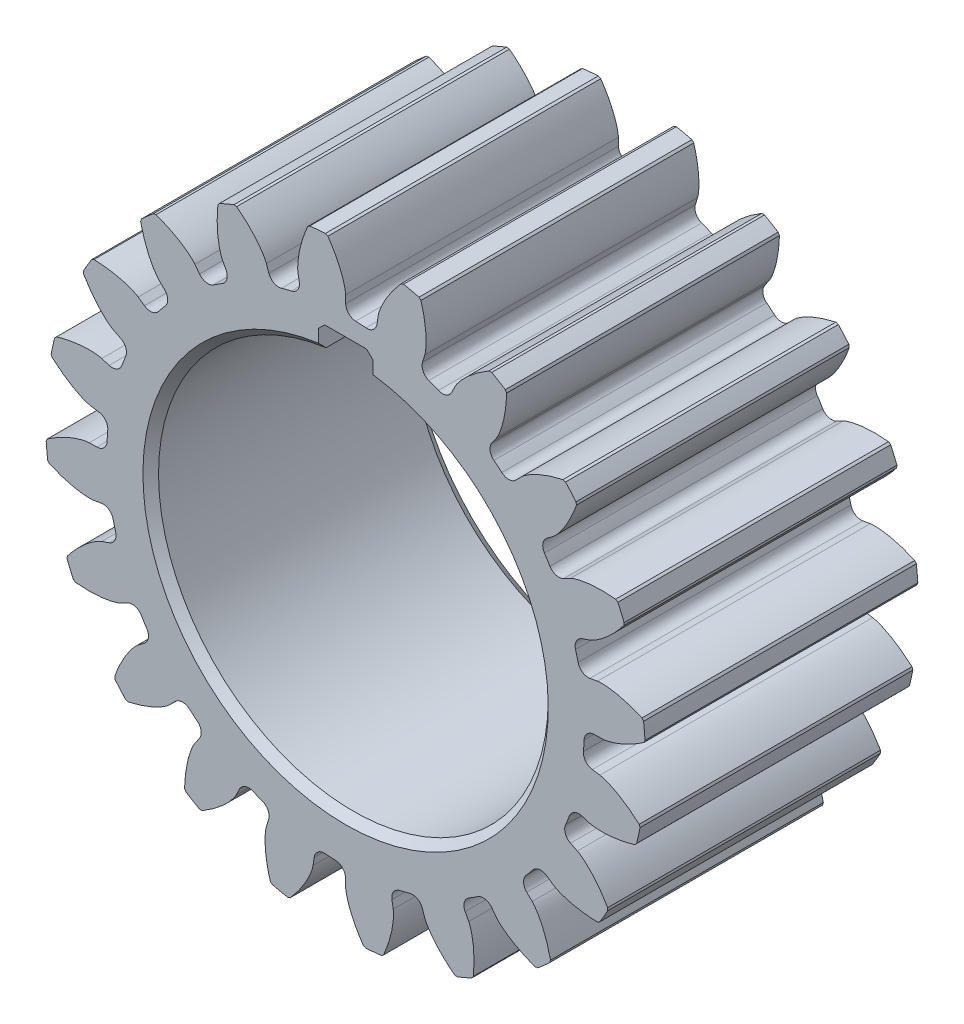
SolidWorks part; units mm, degrees
material "1.6587 (18CrNiMo7-6)"
ref_plane "Front Plane" through (0, 0, 0) normal (0, 0, 1) x (1, 0, 0)
ref_plane "Top Plane" through (0, 0, 0) normal (0, 1, 0) x (1, 0, 0)
ref_plane "Right Plane" through (0, 0, 0) normal (1, 0, 0) x (0, 0, -1)
sketch "Sketch1" plane through (0, 0, 0) normal (0, 0, 1) x (1, 0, 0)
  circle A0 centre (0, 0) radius 35 construction
  circle A1 centre (0, 0) radius 30.625
  dimension "D1" = 70
  dimension "D2" = 4.375
extrude "Boss-Extrude1" add sketch "Sketch1" along normal blind 35
sketch "Sketch2" plane through (0, 0, 0) normal (0, 0, 1) x (1, 0, 0)
  line L0 (32.8892, 0) -> (31.907, -0.0145)
  line L1 (0, 0) -> (34.9961, 0.5217) construction
  line L2 (0, 0) -> (44.1019, 4.1331) construction
  line L3 (32.3165, 6.1109) -> (31.3487, 5.9427)
  circle A0 centre (0, 0) radius 30.625 construction
  arc A1 (30.5979, -1.2884) -> (29.8257, 6.9512) centre (0, 0) ccw
  circle A2 centre (0, 0) radius 35 construction
  arc A3 (38.4264, 2.3799) -> (38.1994, 4.8013) centre (0, 0) ccw
  arc A4 (31.907, -0.0145) -> (30.5979, -1.2884) centre (31.9267, -1.3444) ccw
  arc A5 (31.3487, 5.9427) -> (29.8257, 6.9512) centre (31.121, 7.2531) cw
  circle A6 centre (0, 0) radius 38.5 construction
  spline S0 degree 4 poles (32.8892, 0) (32.9011, 0.0002) (32.9345, 0.0012) (32.9976, 0.0053) (33.1005, 0.0151) (33.2312, 0.0321) (33.3997, 0.0592) (33.5976, 0.0977) (33.8142, 0.147) (34.0488, 0.208) (34.2818, 0.2754) (34.5131, 0.3487) (34.7425, 0.4272) (35.019, 0.5287) (35.3487, 0.6593) (35.7309, 0.8248) (36.1604, 1.0277) (36.5936, 1.2506) (37.016, 1.483) (37.4379, 1.7327) (37.8426, 1.9848) (38.2576, 2.2618) (38.6379, 2.5251) (39.0575, 2.8366) (39.3942, 3.0928) (39.8312, 3.4479) (40.0871, 3.6628) (40.3839, 3.9201) (40.5144, 4.0375) (40.5947, 4.1097) knots 0 0 0 0 0 0.005377 0.015084 0.028532 0.04661 0.064855 0.092111 0.119476 0.146842 0.174209 0.201575 0.228941 0.256307 0.307035 0.361767 0.4165 0.471232 0.525964 0.580697 0.635429 0.690161 0.744894 0.799626 0.854358 0.909091 0.954545 1 1 1 1 1 construction
  spline S1 degree 4 poles (32.8892, 0) (32.9011, 0.0002) (32.9345, 0.0012) (32.9976, 0.0053) (33.1005, 0.0151) (33.2312, 0.0321) (33.3997, 0.0592) (33.5976, 0.0977) (33.8142, 0.147) (34.0488, 0.208) (34.2818, 0.2754) (34.5131, 0.3487) (34.7425, 0.4272) (35.019, 0.5287) (35.3487, 0.6593) (35.7309, 0.8248) (36.1604, 1.0277) (36.5936, 1.2506) (37.016, 1.483) (37.4379, 1.7327) (37.8371, 1.9814) (38.1425, 2.185) (38.3336, 2.3155) (38.4264, 2.3799) knots 0 0 0 0 0 0.005377 0.015084 0.028532 0.04661 0.064855 0.092111 0.119476 0.146842 0.174209 0.201575 0.228941 0.256307 0.307035 0.361767 0.4165 0.471232 0.525964 0.580697 0.635429 0.687158 0.687158 0.687158 0.687158 0.687158
  spline S2 degree 4 poles (32.3165, 6.1109) (32.3282, 6.113) (32.3613, 6.1182) (32.424, 6.1258) (32.5269, 6.1353) (32.6585, 6.1429) (32.8291, 6.1476) (33.0307, 6.1465) (33.2527, 6.1384) (33.4945, 6.122) (33.736, 6.0991) (33.9769, 6.07) (34.2169, 6.0355) (34.5075, 5.9872) (34.8556, 5.9201) (35.2619, 5.8285) (35.7217, 5.7089) (36.1888, 5.5704) (36.647, 5.4206) (37.1079, 5.2536) (37.5464, 5.0834) (37.8843, 4.9401) (38.0963, 4.8474) (38.1994, 4.8013) knots 0 0 0 0 0 0.005377 0.015084 0.028532 0.04661 0.064855 0.092111 0.119476 0.146842 0.174209 0.201575 0.228941 0.256307 0.307035 0.361767 0.4165 0.471232 0.525964 0.580697 0.635429 0.687158 0.687158 0.687158 0.687158 0.687158
  dimension "D1" = 70
  dimension "D3" = 2.66
  dimension "D4" = 4.5
  dimension "D2" = 3.5
extrude "Boss-Extrude2" add sketch "Sketch2" along normal blind 35
chamfer "Chamfer1" distance 0.2 2 edges at (38.1994, 4.8013, 17.5) (38.4264, 2.3799, 17.5)
pattern_circular "CirPattern1" count 20 over 360 about axis through (0, 0, 35) along (0, 0, -1) of "Boss-Extrude2", "Chamfer1"
sketch "Sketch3" plane through (0, 0, 0) normal (0, 0, 1) x (1, 0, 0)
  line L0 (0, 0) -> (0, 28.2) construction
  line L1 (3.5, 24.7538) -> (3.5, 28.2)
  line L2 (-3.5, 24.7538) -> (-3.5, 28.2)
  line L4 (3.5, 28.2) -> (-3.5, 28.2)
  line L5 (3.5, 0) -> (3.5, 28.2) construction
  line L6 (-3.5, 0) -> (-3.5, 28.2) construction
  arc A0 (-3.5, 24.7538) -> (3.5, 24.7538) centre (0, 0) ccw
  dimension "D1" = 50
  dimension "D2" = 28.2
  dimension "D3" = 3.5
  dimension "D4" = 3.5
extrude "Cut-Extrude1" cut sketch "Sketch3" along normal blind 35
chamfer "Chamfer2" distance 1 1 edges at (0, -25, 35)
chamfer "Chamfer3" distance 1.6 1 edges at (0, -25, 0)
chamfer "Chamfer4" distance 0.8 2 edges at (3.5, 28.2, 17.5) (-3.5, 28.2, 17.5)
